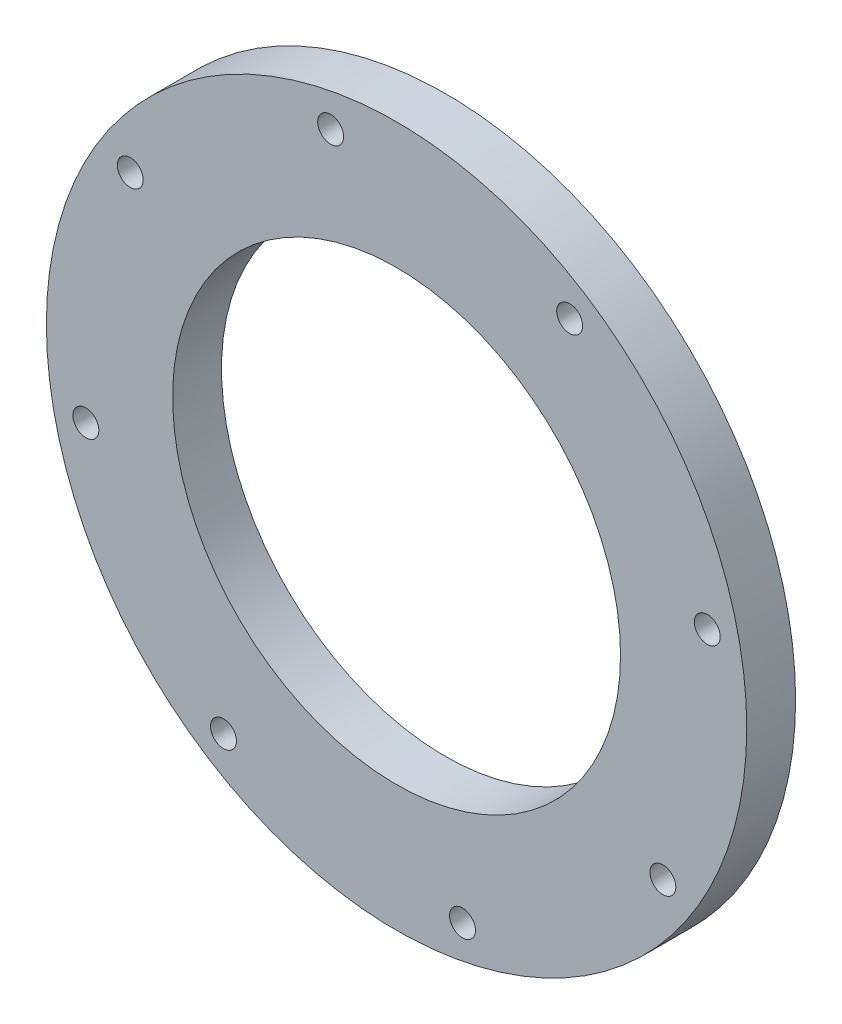
SolidWorks part; units mm, degrees
material "AISI 304"
ref_plane "Front Plane" through (0, 0, 0) normal (0, 0, 1) x (1, 0, 0)
ref_plane "Top Plane" through (0, 0, 0) normal (0, 1, 0) x (1, 0, 0)
ref_plane "Right Plane" through (0, 0, 0) normal (1, 0, 0) x (0, 0, -1)
sketch "Sketch1" plane through (0, 0, 0) normal (0, 0, 1) x (1, 0, 0)
  circle A0 centre (0, 0) radius 54.61
  circle A1 centre (0, 0) radius 34.925
  circle A2 centre (0, 0) radius 54.61 construction
  dimension "D1" = 69.85
extrude "Boss-Extrude1" add sketch "Sketch1" along normal blind 7.62
sketch "Sketch3" plane through (0, 0, 0) normal (0, 0, -1) x (-1, 0, 0)
  circle A0 centre (41.5297, 26.9908) radius 2.0193 construction
  circle A1 centre (10.2805, 48.4513) radius 2.0193 construction
  circle A2 centre (-26.9908, 41.5297) radius 2.0193 construction
  circle A3 centre (-48.4513, 10.2805) radius 2.0193 construction
  circle A4 centre (-41.5297, -26.9908) radius 2.0193 construction
  circle A5 centre (-10.2805, -48.4513) radius 2.0193 construction
  circle A6 centre (26.9908, -41.5297) radius 2.0193 construction
  circle A7 centre (48.4513, -10.2805) radius 2.0193 construction
  circle A8 centre (41.5297, 26.9908) radius 2.0193
  circle A9 centre (10.2805, 48.4513) radius 2.0193
  circle A10 centre (-26.9908, 41.5297) radius 2.0193
  circle A11 centre (-48.4513, 10.2805) radius 2.0193
  circle A12 centre (-41.5297, -26.9908) radius 2.0193
  circle A13 centre (-10.2805, -48.4513) radius 2.0193
  circle A14 centre (26.9908, -41.5297) radius 2.0193
  circle A15 centre (48.4513, -10.2805) radius 2.0193
extrude "Cut-Extrude1" cut sketch "Sketch3" against normal through all
